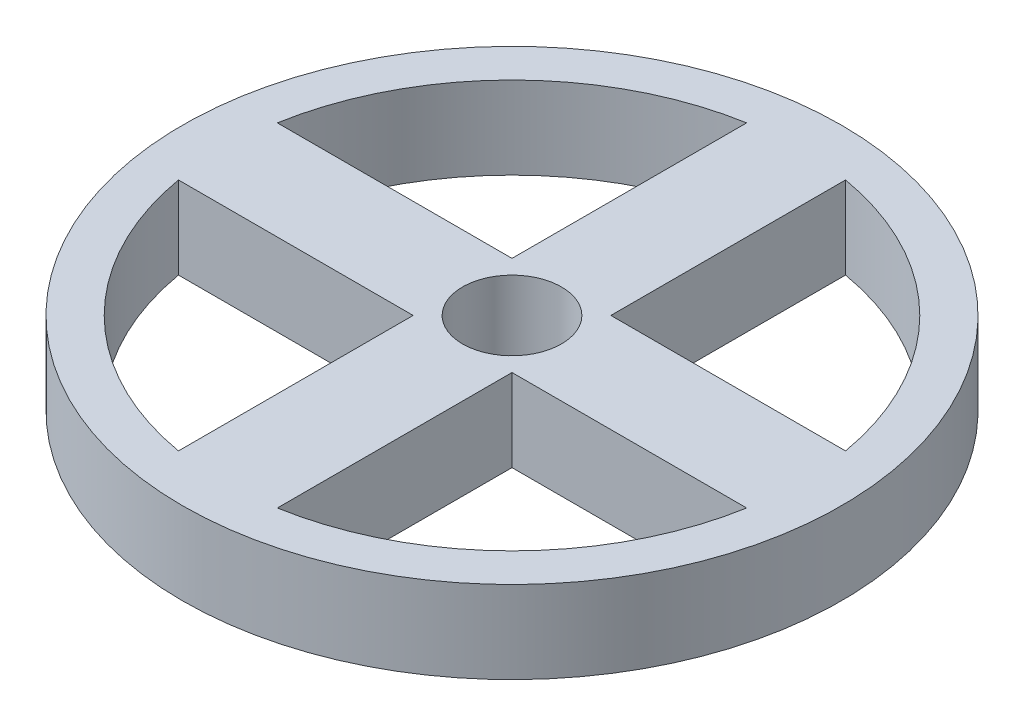
SolidWorks part; units mm, degrees
ref_plane "Front Plane" through (0, 0, 0) normal (0, 0, 1) x (1, 0, 0)
ref_plane "Top Plane" through (0, 0, 0) normal (0, 1, 0) x (1, 0, 0)
ref_plane "Right Plane" through (0, 0, 0) normal (1, 0, 0) x (0, 0, -1)
sketch "Sketch1" plane through (0, 0, 0) normal (0, 1, 0) x (1, 0, 0)
  line L0 (6, 0) -> (6, 34.4819)
  line L1 (-6, 0) -> (-6, 34.4819)
  line L2 (0, 6) -> (34.4819, 6)
  line L3 (0, -6) -> (34.4819, -6)
  line L4 (0, 6) -> (-34.4819, 6)
  line L5 (0, -6) -> (-34.4819, -6)
  line L6 (-6, 0) -> (-6, -34.4819)
  line L7 (6, 0) -> (6, -34.4819)
  circle A0 centre (0, 0) radius 40
  circle A1 centre (0, 0) radius 35
  circle A2 centre (0, 0) radius 6
  dimension "D1" = 80
  dimension "D2" = 70
  dimension "D3" = 12
extrude "Boss-Extrude1" add sketch "Sketch1" along normal blind 10 contours A0 A1 | L4 A1 L5 L6 L1 | L6 A1 L7 L3 L5 | L3 A1 L2 L0 L7 | L0 A1 L1 L4 L2 | A2 L6 L5 | A2 L3 L7 | A2 L0 L2 | A2 L4 L1
